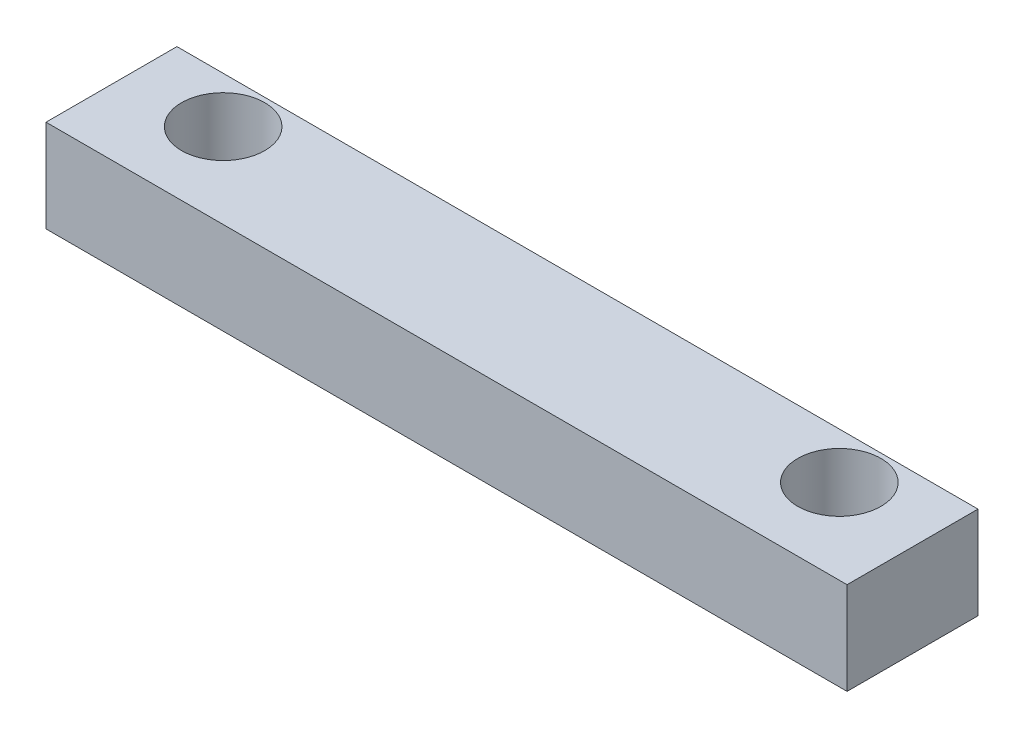
SolidWorks part; units mm, degrees
ref_plane "Front Plane" through (0, 0, 0) normal (0, 0, 1) x (1, 0, 0)
ref_plane "Top Plane" through (0, 0, 0) normal (0, 1, 0) x (1, 0, 0)
ref_plane "Right Plane" through (0, 0, 0) normal (1, 0, 0) x (0, 0, -1)
sketch "Sketch1" plane through (0, 0, 0) normal (0, 1, 0) x (1, 0, 0)
  line L1 (0, 0) -> (26, 0)
  line L2 (0, 0) -> (0, 18)
  line L3 (0, 18) -> (26, 18)
  line L4 (26, 0) -> (26, 18)
  dimension "D1" = 18
  dimension "D2" = 26
extrude "Boss-Extrude1" add sketch "Sketch1" along normal blind 13
sketch "Sketch2" plane through (0, 13, 0) normal (0, 1, 0) x (1, 0, 0)
  line L0 (13, 18) -> (13, 0) construction
  line L1 (3, 15.25) -> (23, 15.25) construction
  line L2 (3, 15.25) -> (3, 2.75) construction
  line L3 (3, 2.75) -> (23, 2.75) construction
  line L4 (23, 15.25) -> (23, 2.75) construction
  line L5 (26, 18) -> (0, 18) construction
  line L6 (0, 0) -> (26, 0) construction
  line L7 (0, 9) -> (26, 9) construction
  line L8 (0, 18) -> (0, 0) construction
  line L9 (26, 0) -> (26, 18) construction
  circle A0 centre (3, 15.25) radius 1.35
  circle A1 centre (23, 15.25) radius 1.35
  circle A2 centre (3, 2.75) radius 1.35
  circle A3 centre (23, 2.75) radius 1.35
  point P16 (3, 9)
  point P17 (13, 15.25)
  dimension "D3" = 2.7
  dimension "D1" = 20
  dimension "D2" = 12.5
extrude "Cut-Extrude1" cut sketch "Sketch2" against normal through all
sketch "Sketch3" plane through (0, 13, 0) normal (0, 1, 0) x (1, 0, 0)
  line L0 (26, 0) -> (26, 18) construction
  line L1 (0, 18) -> (26, 18)
  line L2 (0, 18) -> (0, 4.25)
  line L3 (0, 4.25) -> (26, 4.25)
  line L4 (26, 18) -> (26, 4.25)
  circle A1 centre (3, 2.75) radius 1.35 construction
  dimension "D1" = 1.5
extrude "Cut-Extrude3" cut sketch "Sketch3" against normal through all
sketch "Sketch4" plane through (0, 0, 0) normal (0, 0, 1) x (1, 0, 0)
  line L0 (26, 13) -> (26, 0) construction
  line L1 (0, 0) -> (26, 0)
  line L2 (0, 0) -> (0, 10)
  line L3 (0, 10) -> (26, 10)
  line L4 (26, 0) -> (26, 10)
  line L5 (0, 13) -> (26, 13) construction
  dimension "D1" = 3
extrude "Cut-Extrude4" cut sketch "Sketch4" against normal through all
